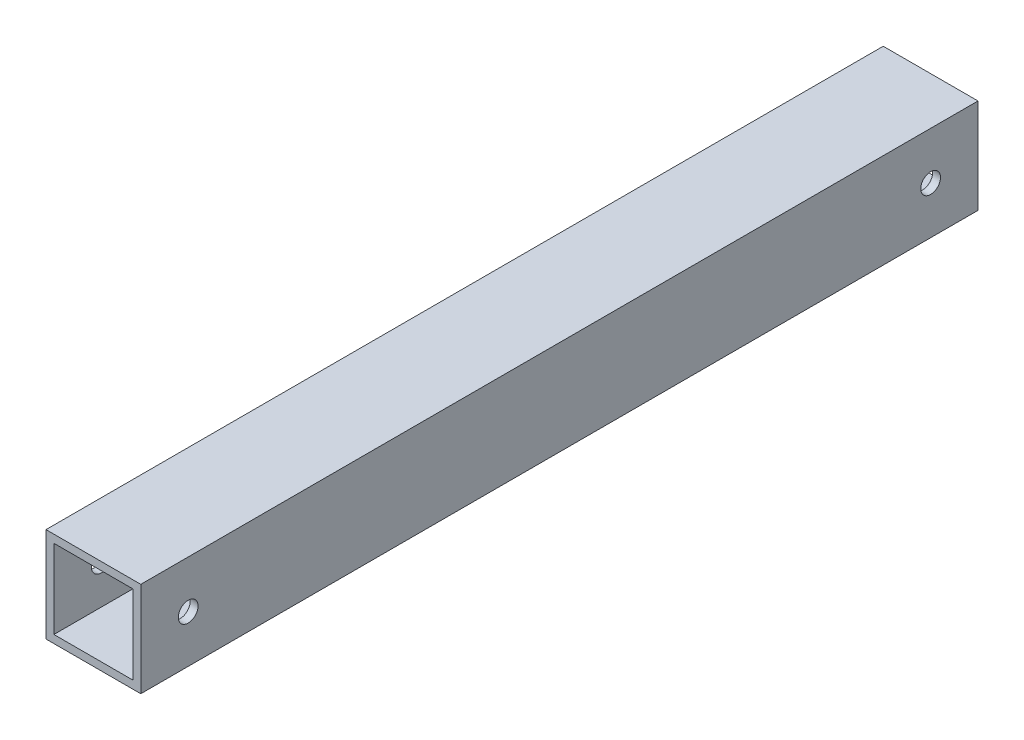
SolidWorks part; units mm, degrees
ref_plane "Front Plane" through (0, 0, 0) normal (0, 0, 1) x (1, 0, 0)
ref_plane "Top Plane" through (0, 0, 0) normal (0, 1, 0) x (1, 0, 0)
ref_plane "Right Plane" through (0, 0, 0) normal (1, 0, 0) x (0, 0, -1)
sketch "Sketch1" plane through (0, 0, 0) normal (0, 0, 1) x (1, 0, 0)
  line L1 (-38.1, -38.1) -> (38.1, -38.1)
  line L2 (-38.1, -38.1) -> (-38.1, 38.1)
  line L3 (-38.1, 38.1) -> (38.1, 38.1)
  line L4 (38.1, -38.1) -> (38.1, 38.1)
  line L5 (-38.1, -38.1) -> (38.1, 38.1) construction
  line L6 (-38.1, 38.1) -> (38.1, -38.1) construction
  line L7 (-31.75, -31.75) -> (31.75, -31.75)
  line L8 (-31.75, -31.75) -> (-31.75, 31.75)
  line L9 (-31.75, 31.75) -> (31.75, 31.75)
  line L10 (31.75, -31.75) -> (31.75, 31.75)
  line L11 (-31.75, -31.75) -> (31.75, 31.75) construction
  line L12 (-31.75, 31.75) -> (31.75, -31.75) construction
  point P0 (0, 0)
  point P6 (0, 0)
  dimension "D1" = 6.35
  dimension "D2" = 76.2
extrude "Boss-Extrude1" add sketch "Sketch1" along normal mid plane 673.1
sketch "Sketch2" plane through (38.1, 0, 0) normal (1, 0, 0) x (0, 0, -1)
  line L0 (336.55, 0) -> (298.45, 0) construction
  line L1 (336.55, -38.1) -> (336.55, 38.1) construction
  circle A0 centre (298.45, 0) radius 7.9375
  dimension "D1" = 15.875
  dimension "D2" = 38.1
extrude "Cut-Extrude1" cut sketch "Sketch2" against normal through all
mirror "Mirror1" about plane through (0, 0, 0) normal (0, 0, 1) of "Cut-Extrude1"
